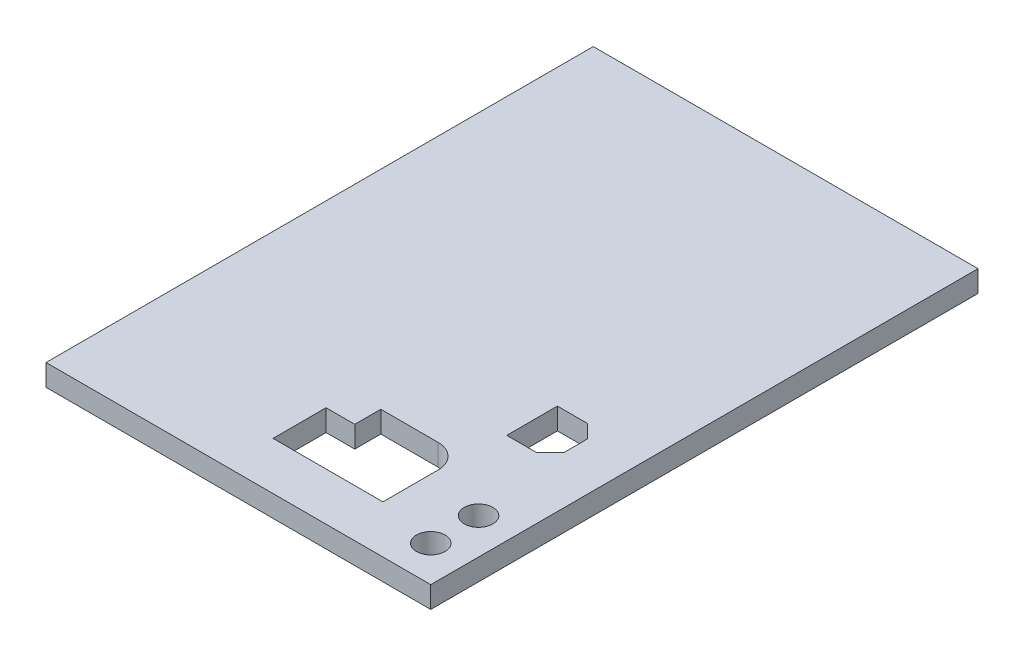
SolidWorks part; units mm, degrees
material "Perspex (TM) GS Acrylic Cast Sheet"
ref_plane "Front Plane" through (0, 0, 0) normal (0, 0, 1) x (1, 0, 0)
ref_plane "Top Plane" through (0, 0, 0) normal (0, 1, 0) x (1, 0, 0)
ref_plane "Right Plane" through (0, 0, 0) normal (1, 0, 0) x (0, 0, -1)
sketch "Sketch1" plane through (0, 0, 0) normal (0, 1, 0) x (1, 0, 0)
  line L1 (-80.5, -114.5) -> (80.5, -114.5)
  line L2 (-80.5, -114.5) -> (-80.5, 114.5)
  line L3 (-80.5, 114.5) -> (80.5, 114.5)
  line L4 (80.5, -114.5) -> (80.5, 114.5)
  line L5 (-80.5, -114.5) -> (80.5, 114.5) construction
  line L6 (-80.5, 114.5) -> (80.5, -114.5) construction
  point P0 (0, 0)
  dimension "D1" = 161
  dimension "D2" = 229
extrude "Boss-Extrude1" add sketch "Sketch1" along normal blind 9
sketch "Sketch2" plane through (0, 9, 0) normal (0, 1, 0) x (1, 0, 0)
  line L0 (65.5, -79.5) -> (65.5, -99.5) construction
  line L1 (80.5, -114.5) -> (80.5, 114.5) construction
  line L6 (-80.5, -114.5) -> (80.5, -114.5) construction
  line L8 (40.5, -94.5) -> (-5.5, -94.5)
  line L10 (6.5, -72.3) -> (-5.5, -72.3)
  line L11 (-5.5, -94.5) -> (-5.5, -72.3)
  line L17 (42.3, -23.3) -> (54.9, -23.3)
  line L18 (42.3, -23.3) -> (42.3, -44.5)
  line L19 (42.3, -44.5) -> (54.9, -44.5)
  line L25 (54.9, -44.5) -> (60.5, -38.9)
  line L26 (60.5, -38.9) -> (60.5, -28.9)
  line L27 (60.5, -28.9) -> (54.9, -23.3)
  line L28 (40.5, -94.5) -> (40.5, -71.4)
  line L33 (30.5, -61.4) -> (6.5, -61.4)
  line L34 (6.5, -61.4) -> (6.5, -72.3)
  line L35 (-80.5, 114.5) -> (-80.5, -114.5) construction
  circle A1 centre (65.5, -99.5) radius 6
  circle A2 centre (65.5, -79.5) radius 6
  arc A3 (40.5, -71.4) -> (30.5, -61.4) centre (30.5, -71.4) ccw
  point P2 (11.9831, -72.3)
  point P13 (40.5, -61.4)
  point P14 (39.9248, -71.4)
  point P17 (0, 0)
  dimension "D19" = 12
  dimension "D23" = 10
  dimension "D3" = 20
  dimension "D4" = 46
  dimension "D5" = 33.1
  dimension "D6" = 12
  dimension "D9" = 135
  dimension "D10" = 70
  dimension "D15" = 20
  dimension "D16" = 18.2
  dimension "D17" = 21.2
  dimension "D18" = 10
  dimension "D20" = 20
  dimension "D21" = 15
  dimension "D22" = 15
  dimension "D24" = 75
  dimension "D30" = 22.2
extrude "Cut-Extrude1" cut sketch "Sketch2" against normal through all
equation "\"PCLength\"= 143mm'Length across I/O from PS to GPU"
equation "\"PCWidth\"= 340mm'Distance of longest part parallel to GPU(ussually GPU)"
equation "\"PCHeight\"= 190mm'Tallest point with mobo laying flat"
equation "\"WallThickness\"= 9mm'Thickness of each outer tank wall"
equation "\"ThermoBarrierThickness\"= 6mm'Thickness of barrier between hot side and cold side"
equation "\"HotSideGap\"= 15mm'Space in the hot side that hot fluid flows into"
equation "\"PCClearance\"= 40mm'Clearance from top of tank to top of PC"
equation "\"RadiatorHeight\"= 277.37mm'Final Height from ground of radiators"
equation "\"AirflowGap\"= 26mm'Distance between radiators and tank for airflow"
equation "\"VolumeSubtraction\"= 230mm"
equation "\"D1@Sketch1\"=\"PCLength\" + (2 * \"WallThickness\")"
equation "\"D1@Boss-Extrude1\"=\"WallThickness\""
equation "\"D2@Sketch1\"=\"PCHeight\" + \"ThermoBarrierThickness\" + \"HotSideGap\" + (2 * \"WallThickness\")"
